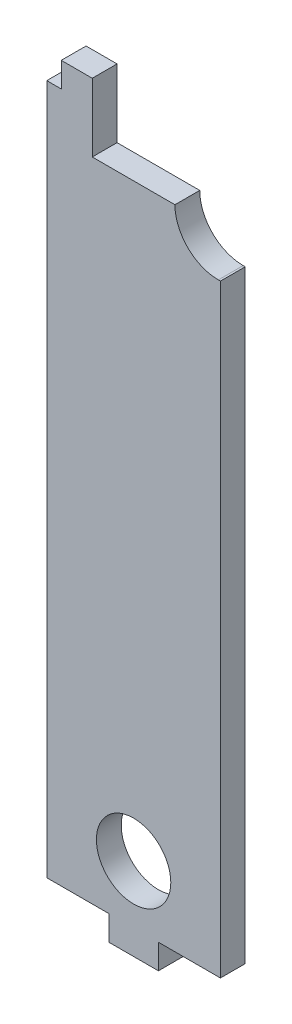
SolidWorks part; units mm, degrees
ref_plane "Front Plane" through (0, 0, 0) normal (0, 0, 1) x (1, 0, 0)
ref_plane "Top Plane" through (0, 0, 0) normal (0, 1, 0) x (1, 0, 0)
ref_plane "Right Plane" through (0, 0, 0) normal (1, 0, 0) x (0, 0, -1)
sketch "Sketch2" plane through (0, 0, 0) normal (0, 1, 0) x (1, 0, 0)
  line L0 (0, 0) -> (0, 6) construction
  dimension "D1" = 6
sketch "Sketch1" plane through (0, 0, 0) normal (0, 0, 1) x (1, 0, 0)
  line L0 (10, 83.5) -> (10, 73)
  line L1 (-21, -83.5) -> (21, -83.5)
  line L2 (-21, -83.5) -> (-21, 83.5)
  line L3 (-21, 83.5) -> (21, 83.5)
  line L4 (21, -83.5) -> (21, 83.5)
  line L5 (-21, -83.5) -> (21, 83.5) construction
  line L6 (-21, 83.5) -> (21, -83.5) construction
  line L7 (10, 73) -> (-10, 73)
  line L8 (-10, 73) -> (-10, 83.5)
  line L9 (0, 73) -> (0, 83.5) construction
  line L10 (20.5, 62.5) -> (21, 62.5)
  line L11 (-17.5, 83.5) -> (-23.5, 83.5)
  line L12 (-21, -83.5) -> (-23.5, -83.5) construction
  line L13 (-23.5, -83.5) -> (-23.5, 83.5) construction
  line L14 (-23.5, 83.5) -> (-21, 83.5) construction
  line L15 (-17.5, 83.5) -> (-17.5, 89.5)
  line L16 (-17.5, 89.5) -> (-10, 89.5)
  line L17 (-10, 89.5) -> (-10, 83.5)
  line L18 (0, -83.5) -> (0, -69.5) construction
  line L19 (-6, -83.5) -> (-6, -89.5)
  line L20 (-6, -89.5) -> (6, -89.5)
  line L21 (6, -89.5) -> (6, -83.5)
  line L22 (0, -89.5) -> (0, -83.5)
  line L23 (20.5, 73) -> (20.5, 62.5) construction
  line L24 (20.5, 73) -> (10, 73) construction
  circle A0 centre (0, -69.5) radius 9
  arc A1 (10, 73) -> (20.5, 62.5) centre (20.5, 73) ccw
  point P0 (0, 0)
  point P13 (-17.5, 83.5)
  dimension "D9" = 18
  dimension "D1" = 167
  dimension "D2" = 42
  dimension "D3" = 10.5
  dimension "D4" = 20
  dimension "D6" = 2.5
  dimension "D7" = 6
  dimension "D8" = 6
  dimension "D10" = 12
  dimension "D11" = 20
extrude "Boss-Extrude1" add sketch "Sketch1" against normal up to vertex (6 mm away)
equation "\"t_wood\"= 6' Thickness of the wood"
equation "\"t_glass\"= 2.5'Thickness of glass panels"
equation "\"w_glass\"= 248"
equation "\"h_glass\"= 167"
equation "\"h_food_internal\" = 60"
equation "\"entry_height\"= 20"
equation "\"entry diameter\"= 8"
equation "\"glass_bottom_overlap\"= 8"
equation "\"default_finger_size\"= 12"
equation "\"brood_depth\"= 42"
equation "\"outer_box_depth\" = \"brood_depth\" + ( 2 * \"t_glass\" ) + ( 2 * \"t_wood\" )"
equation "\"outer_box_width\"= \"w_glass\" + ( 2 * \"t_wood\" )"
equation "\"food_top_clearance\"= 10"
equation "\"outer_box_height\"= \"t_wood\" + \"h_glass\" + \"t_wood\" + \"h_food_internal\" + \"food_top_clearance\" + \"t_wood\""
equation "\"food_internal_depth\"= \"brood_depth\" + \"t_glass\" + \"t_glass\" - \"t_wood\" - \"t_wood\""
equation "\"food_channel_clearance_width\"= 14"
equation "\"bar_top_play\"= 4.5"
equation "\"bar_entry_angle\"= 10"
equation "\"bar_width\"= 20"
equation "\"entry_disk_play\"= 0.3"
equation "\"D1@Sketch2\"=\"t_wood\""
equation "\"D1@Sketch1\"=\"h_glass\""
equation "\"D2@Sketch1\"=\"brood_depth\""
equation "\"D3@Sketch1\"=\"bar_top_play\"+\"t_wood\""
equation "\"D4@Sketch1\"=\"bar_width\""
equation "\"D6@Sketch1\"=\"t_glass\""
equation "\"D7@Sketch1\"=\"t_wood\""
equation "\"D9@Sketch1\"=\"entry diameter\" +10"
equation "\"D8@Sketch1\"=\"t_wood\""
equation "\"D10@Sketch1\"=\"default_finger_size\""
equation "\"D11@Sketch1\"=\"entry_height\""
